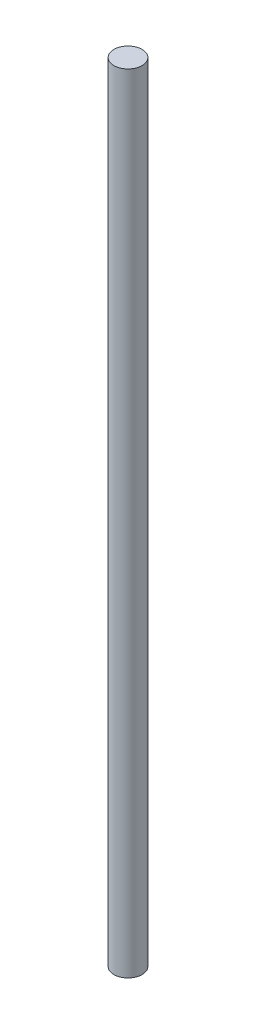
SolidWorks part; units mm, degrees
ref_plane "Front Plane" through (0, 0, 0) normal (0, 0, 1) x (1, 0, 0)
ref_plane "Top Plane" through (0, 0, 0) normal (0, 1, 0) x (1, 0, 0)
ref_plane "Right Plane" through (0, 0, 0) normal (1, 0, 0) x (0, 0, -1)
sketch "Sketch1" plane through (0, 0, 0) normal (0, 1, 0) x (1, 0, 0)
  circle A0 centre (0, 0) radius 3.175
  dimension "D1" = 6.35
extrude "Boss-Extrude1" add sketch "Sketch1" along normal blind 177.8
